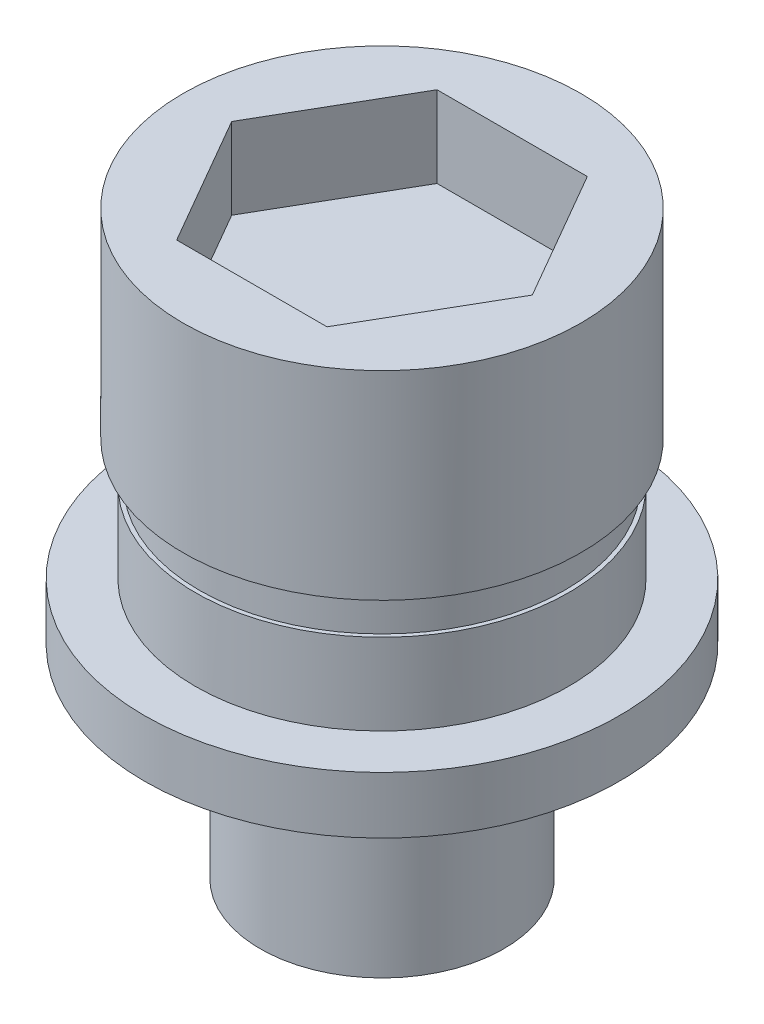
SolidWorks part; units mm, degrees
ref_plane "前视基准面" through (0, 0, 0) normal (0, 0, 1) x (1, 0, 0)
ref_plane "上视基准面" through (0, 0, 0) normal (0, 1, 0) x (1, 0, 0)
ref_plane "右视基准面" through (0, 0, 0) normal (1, 0, 0) x (0, 0, -1)
sketch "草图1" plane through (0, 0, 0) normal (0, 1, 0) x (1, 0, 0)
  circle A0 centre (0, 0) radius 5.85
  dimension "D1" = 11.7
extrude "凸台-拉伸1" add sketch "草图1" along normal blind 1.4
sketch "草图2" plane through (0, 1.4, 0) normal (0, 1, 0) x (1, 0, 0)
  circle A0 centre (0, 0) radius 4.6
  dimension "D1" = 9.2
extrude "凸台-拉伸2" add sketch "草图2" along normal blind 2
sketch "草图3" plane through (0, 3.4, 0) normal (0, 1, 0) x (1, 0, 0)
  circle A0 centre (0, 0) radius 4.9
  dimension "D1" = 9.8
extrude "凸台-拉伸3" add sketch "草图3" along normal blind 5.9
sketch "草图4" plane through (0, 3.4, 0) normal (0, -1, 0) x (1, 0, 0)
  circle A0 centre (0, 0) radius 4.5
  circle A1 centre (0, 0) radius 10.5263
  dimension "D1" = 9
extrude "切除-拉伸1" cut sketch "草图4" against normal blind 1
sketch "草图5" plane through (0, 9.3, 0) normal (0, 1, 0) x (1, 0, 0)
  line L1 (-3.7026, 0) -> (-1.8513, -3.2065)
  line L2 (-1.8513, -3.2065) -> (1.8513, -3.2065)
  line L3 (1.8513, -3.2065) -> (3.7026, 0)
  line L4 (3.7026, 0) -> (1.8513, 3.2065)
  line L5 (1.8513, 3.2065) -> (-1.8513, 3.2065)
  line L6 (-1.8513, 3.2065) -> (-3.7026, 0)
  circle A0 centre (0, 0) radius 3.2065 construction
extrude "切除-拉伸2" cut sketch "草图5" against normal blind 2
sketch "草图6" plane through (0, 0, 0) normal (0, -1, 0) x (1, 0, 0)
  circle A0 centre (0, 0) radius 3
  dimension "D1" = 6
extrude "凸台-拉伸4" add sketch "草图6" along normal blind 5
